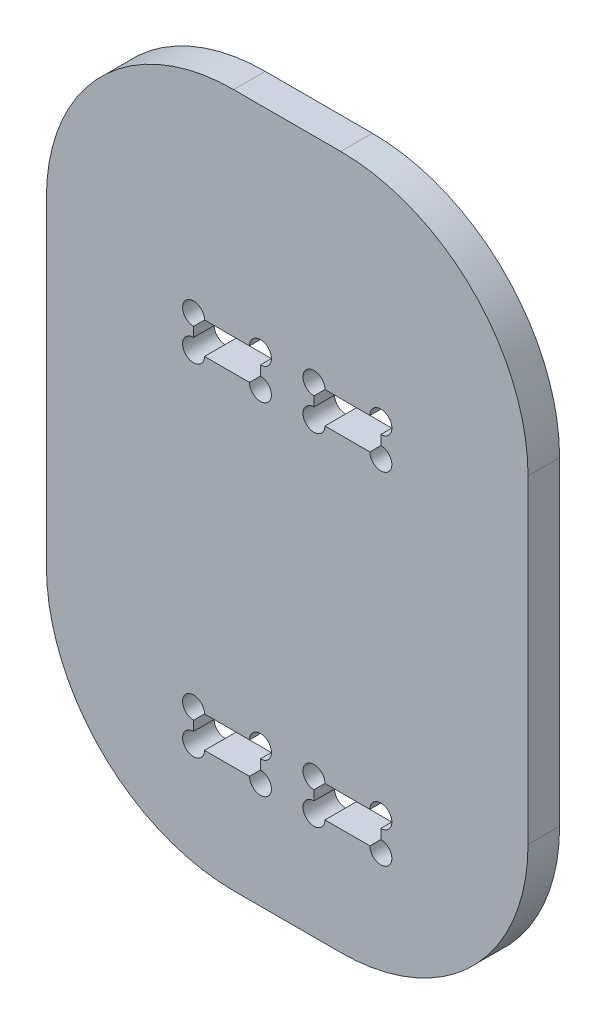
SolidWorks part; units mm, degrees
ref_plane "Front Plane" through (0, 0, 0) normal (0, 0, 1) x (1, 0, 0)
ref_plane "Top Plane" through (0, 0, 0) normal (0, 1, 0) x (1, 0, 0)
ref_plane "Right Plane" through (0, 0, 0) normal (1, 0, 0) x (0, 0, -1)
sketch "Sketch1" plane through (0, 0, 0) normal (0, 0, 1) x (1, 0, 0)
  line L0 (-17.5, 17.325) -> (17.5, 17.325) construction
  line L37 (-17.5, 17.325) -> (-17.5, -52.325) construction
  line L38 (-17.5, -52.325) -> (17.5, -52.325) construction
  line L39 (17.5, 17.325) -> (17.5, -52.325) construction
  line L40 (-17.5, 17.325) -> (17.5, -52.325) construction
  line L41 (-17.5, -52.325) -> (17.5, 17.325) construction
  line L42 (-17.5, 17.325) -> (-5, 17.325)
  line L43 (-17.5, 17.325) -> (-17.5, 11.425)
  line L44 (-17.5, 11.425) -> (-5, 11.425)
  line L45 (-5, 17.325) -> (-5, 11.425)
  line L46 (-17.5, 17.325) -> (-5, 11.425) construction
  line L47 (-17.5, 11.425) -> (-5, 17.325) construction
  line L48 (17.5, 17.325) -> (5, 17.325)
  line L49 (17.5, 17.325) -> (17.5, 11.425)
  line L50 (17.5, 11.425) -> (5, 11.425)
  line L51 (5, 17.325) -> (5, 11.425)
  line L52 (17.5, 17.325) -> (5, 11.425) construction
  line L53 (17.5, 11.425) -> (5, 17.325) construction
  line L54 (-45, -77.325) -> (45, -77.325)
  line L55 (17.5, -52.325) -> (5, -52.325)
  line L56 (17.5, -52.325) -> (17.5, -46.425)
  line L57 (17.5, -46.425) -> (5, -46.425)
  line L58 (5, -52.325) -> (5, -46.425)
  line L59 (17.5, -52.325) -> (5, -46.425) construction
  line L60 (17.5, -46.425) -> (5, -52.325) construction
  line L61 (-17.5, -52.325) -> (-5, -52.325)
  line L62 (-17.5, -52.325) -> (-17.5, -46.425)
  line L63 (-17.5, -46.425) -> (-5, -46.425)
  line L64 (-5, -52.325) -> (-5, -46.425)
  line L65 (-17.5, -52.325) -> (-5, -46.425) construction
  line L66 (-17.5, -46.425) -> (-5, -52.325) construction
  line L67 (-45, -77.325) -> (-45, 77.325)
  line L68 (-45, 77.325) -> (45, 77.325)
  line L69 (45, -77.325) -> (45, 77.325)
  line L70 (-45, -77.325) -> (45, 77.325) construction
  line L71 (-45, 77.325) -> (45, -77.325) construction
  point P30 (0, -17.5)
  point P32 (0, 0)
  point P35 (-11.25, 14.375)
  point P40 (11.25, 14.375)
  point P46 (11.25, -49.375)
  point P51 (-11.25, -49.375)
  dimension "D8" = 12.5
  dimension "D9" = 5.9
  dimension "D6" = 25
  dimension "D7" = 90
  dimension "D10" = 60
  dimension "D14" = 35
  dimension "D2" = 57.85
extrude "Boss-Extrude1" add sketch "Sketch1" along normal blind 5.9
fillet "Fillet2" radius 10 4 edges at (-45, -77.325, 2.95) (45, -77.325, 2.95) (45, 77.325, 2.95) (-45, 77.325, 2.95)
sketch "Sketch2" plane through (0, 0, 5.9) normal (0, 0, 1) x (1, 0, 0)
  line L0 (0, 0) -> (0, 77.325) construction
  line L1 (35, 77.325) -> (-35, 77.325) construction
  line L2 (-35, -77.325) -> (35, -77.325) construction
  line L3 (-10, -119.325) -> (10, -119.325) construction
  line L4 (-10, -119.325) -> (-10, -77.325) construction
  line L5 (-10, -77.325) -> (10, -77.325)
  line L6 (10, -119.325) -> (10, -77.325) construction
  line L7 (-10, -119.325) -> (10, -77.325) construction
  line L8 (-10, -77.325) -> (10, -119.325) construction
  line L17 (-48.9991, 110.2179) -> (-31.9041, 120.5986) construction
  line L18 (-48.9991, 110.2179) -> (-45.9144, 105.1379) construction
  line L19 (-31.9041, 120.5986) -> (-8.5475, 82.1347) construction
  line L23 (0, 77.325) -> (-13.9683, 77.325)
  line L25 (-45, 53.4823) -> (0, 77.325)
  line L26 (-45, 67.325) -> (-45, -67.325) construction
  line L33 (-38.5879, 93.0726) -> (-44.298, 113.0726)
  line L34 (-44.298, 113.0726) -> (-36.6052, 117.7439)
  line L35 (-36.6052, 117.7439) -> (-15.6534, 93.8367)
  line L36 (-15.6534, 93.8367) -> (-8.5475, 82.1347)
  line L38 (-10, -103.2393) -> (-4.5, -119.325)
  line L39 (-4.5, -119.325) -> (4.5, -119.325)
  line L40 (4.5, -119.325) -> (10, -103.2393)
  line L49 (-24.6, -77.325) -> (-10, -90.9393)
  line L50 (-10, -90.9393) -> (-10, -103.2393)
  line L51 (10, -103.2393) -> (10, -90.9393)
  line L52 (10, -90.9393) -> (24.6, -77.325)
  line L53 (-24.6, -77.325) -> (-10, -77.325)
  line L54 (10, -77.325) -> (24.6, -77.325)
  line L55 (-45, 53.4823) -> (-45, 67.325)
  line L57 (-38.5879, 93.0726) -> (-31.9704, 80.2418)
  line L58 (-35, 77.325) -> (-33.7479, 77.325)
  line L59 (45, 53.4823) -> (0, 77.325)
  line L60 (45, 53.4823) -> (45, 67.325)
  line L61 (35, 77.325) -> (33.7479, 77.325)
  line L62 (38.5879, 93.0726) -> (31.9704, 80.2418)
  line L63 (38.5879, 93.0726) -> (44.298, 113.0726)
  line L64 (44.298, 113.0726) -> (36.6052, 117.7439)
  line L65 (36.6052, 117.7439) -> (15.6534, 93.8367)
  line L66 (15.6534, 93.8367) -> (8.5475, 82.1347)
  arc A0 (-8.5475, 82.1347) -> (8.5475, 82.1347) centre (0, 87.325) ccw
  arc A4 (-35, 77.325) -> (-45, 67.325) centre (-35, 67.325) ccw construction
  arc A5 (-35, 77.325) -> (-45, 67.325) centre (-35, 67.325) ccw
  arc A6 (-31.9704, 80.2418) -> (-33.7479, 77.325) centre (-33.7479, 79.325) cw
  arc A7 (45, 67.325) -> (35, 77.325) centre (35, 67.325) ccw construction
  arc A8 (45, 67.325) -> (35, 77.325) centre (35, 67.325) ccw
  arc A9 (35, 77.325) -> (45, 67.325) centre (35, 67.325) cw
  arc A10 (31.9704, 80.2418) -> (33.7479, 77.325) centre (33.7479, 79.325) ccw
  point P5 (0, -98.325)
  point P13 (-40.4516, 115.4082)
  point P31 (0, -119.325)
  point P54 (-60, 0)
  dimension "D3" = 10
  dimension "D4" = 20
  dimension "D8" = 2
  dimension "D1" = 20
  dimension "D2" = 42
  dimension "D5" = 20
  dimension "D6" = 45
  dimension "D7" = 9
  dimension "D9" = 9
  dimension "D10" = 17
  dimension "D12" = 12.3
  dimension "D13" = 14.6
  dimension "D14" = 60
extrude "Boss-Extrude2" add sketch "Sketch2" against normal up to surface (5.9 mm away) up to face at (0, 0, 0)
sketch "Sketch4" plane through (0, 0, 5.9) normal (0, 0, 1) x (1, 0, 0)
  line L5 (0, 76.425) -> (0, 0) construction
sketch "Sketch5" plane through (0, 0, 5.9) normal (0, 0, 1) x (1, 0, 0)
  circle A0 centre (-17.5, 11.425) radius 2.05
  circle A1 centre (-5, 11.425) radius 2.05
  circle A2 centre (-5, 17.325) radius 2.05
  circle A3 centre (-17.5, 17.325) radius 2.05
  circle A4 centre (17.5, 11.425) radius 2.05
  circle A5 centre (17.5, 17.325) radius 2.05
  circle A6 centre (5, 17.325) radius 2.05
  circle A7 centre (5, 11.425) radius 2.05
  circle A8 centre (5, -52.325) radius 2.05
  circle A9 centre (17.5, -52.325) radius 2.05
  circle A10 centre (17.5, -46.425) radius 2.05
  circle A11 centre (5, -46.425) radius 2.05
  circle A12 centre (-5, -46.425) radius 2.05
  circle A13 centre (-5, -52.325) radius 2.05
  circle A14 centre (-17.5, -52.325) radius 2.05
  circle A15 centre (-17.5, -46.425) radius 2.05
  dimension "D1" = 4.1
extrude "Cut-Extrude1" cut sketch "Sketch5" against normal up to next
sketch "Sketch7" plane through (0, 0, 5.9) normal (0, 0, 1) x (1, 0, 0)
  line L0 (-45, 67.325) -> (-45, -67.325) construction
  line L1 (-45, -72.325) -> (45, -72.325)
  line L2 (-45, -72.325) -> (-45, 57.325)
  line L3 (-45, 57.325) -> (45, 57.325)
  line L4 (45, -72.325) -> (45, 57.325)
  line L5 (-45, -72.325) -> (45, 57.325) construction
  line L6 (-45, 57.325) -> (45, -72.325) construction
  line L7 (45, -67.325) -> (45, 67.325) construction
  line L8 (24.6, -77.325) -> (35, -77.325) construction
  line L9 (-33.7479, 77.325) -> (-35, 77.325) construction
  line L33 (-45, 67.325) -> (-45, -67.325)
  line L34 (-35, -77.325) -> (-24.6, -77.325)
  line L35 (-24.6, -77.325) -> (-10, -90.9393)
  line L36 (-10, -90.9393) -> (-10, -103.2393)
  line L37 (-10, -103.2393) -> (-4.5, -119.325)
  line L38 (-4.5, -119.325) -> (4.5, -119.325)
  line L39 (4.5, -119.325) -> (10, -103.2393)
  line L40 (10, -103.2393) -> (10, -90.9393)
  line L41 (10, -90.9393) -> (24.6, -77.325)
  line L42 (24.6, -77.325) -> (35, -77.325)
  line L43 (45, -67.325) -> (45, 67.325)
  line L44 (35, 77.325) -> (33.7479, 77.325)
  line L45 (31.9704, 80.2418) -> (38.5879, 93.0726)
  line L46 (38.5879, 93.0726) -> (44.298, 113.0726)
  line L47 (44.298, 113.0726) -> (36.6052, 117.7439)
  line L48 (36.6052, 117.7439) -> (15.6534, 93.8367)
  line L49 (15.6534, 93.8367) -> (8.5475, 82.1347)
  line L50 (-8.5475, 82.1347) -> (-15.6534, 93.8367)
  line L51 (-15.6534, 93.8367) -> (-36.6052, 117.7439)
  line L52 (-36.6052, 117.7439) -> (-44.298, 113.0726)
  line L53 (-44.298, 113.0726) -> (-38.5879, 93.0726)
  line L54 (-38.5879, 93.0726) -> (-31.9704, 80.2418)
  line L55 (-33.7479, 77.325) -> (-35, 77.325)
  line L56 (-45, 67.325) -> (-45, -67.325)
  line L57 (-35, -77.325) -> (-24.6, -77.325)
  line L58 (-24.6, -77.325) -> (-10, -90.9393)
  line L59 (-10, -90.9393) -> (-10, -103.2393)
  line L60 (-10, -103.2393) -> (-4.5, -119.325)
  line L61 (-4.5, -119.325) -> (4.5, -119.325)
  line L62 (4.5, -119.325) -> (10, -103.2393)
  line L63 (10, -103.2393) -> (10, -90.9393)
  line L64 (10, -90.9393) -> (24.6, -77.325)
  line L65 (24.6, -77.325) -> (35, -77.325)
  line L66 (45, -67.325) -> (45, 67.325)
  line L67 (35, 77.325) -> (33.7479, 77.325)
  line L68 (31.9704, 80.2418) -> (38.5879, 93.0726)
  line L69 (38.5879, 93.0726) -> (44.298, 113.0726)
  line L70 (44.298, 113.0726) -> (36.6052, 117.7439)
  line L71 (36.6052, 117.7439) -> (15.6534, 93.8367)
  line L72 (15.6534, 93.8367) -> (8.5475, 82.1347)
  line L73 (-8.5475, 82.1347) -> (-15.6534, 93.8367)
  line L74 (-15.6534, 93.8367) -> (-36.6052, 117.7439)
  line L75 (-36.6052, 117.7439) -> (-44.298, 113.0726)
  line L76 (-44.298, 113.0726) -> (-38.5879, 93.0726)
  line L77 (-38.5879, 93.0726) -> (-31.9704, 80.2418)
  line L78 (-33.7479, 77.325) -> (-35, 77.325)
  arc A7 (-45, -67.325) -> (-35, -77.325) centre (-35, -67.325) ccw
  arc A8 (35, -77.325) -> (45, -67.325) centre (35, -67.325) ccw
  arc A9 (45, 67.325) -> (35, 77.325) centre (35, 67.325) ccw
  arc A10 (31.9704, 80.2418) -> (33.7479, 77.325) centre (33.7479, 79.325) ccw
  arc A11 (-8.5475, 82.1347) -> (8.5475, 82.1347) centre (0, 87.325) ccw
  arc A12 (-33.7479, 77.325) -> (-31.9704, 80.2418) centre (-33.7479, 79.325) ccw
  arc A13 (-35, 77.325) -> (-45, 67.325) centre (-35, 67.325) ccw
  arc A14 (-45, -67.325) -> (-35, -77.325) centre (-35, -67.325) ccw
  arc A15 (35, -77.325) -> (45, -67.325) centre (35, -67.325) ccw
  arc A16 (45, 67.325) -> (35, 77.325) centre (35, 67.325) ccw
  arc A17 (31.9704, 80.2418) -> (33.7479, 77.325) centre (33.7479, 79.325) ccw
  arc A18 (-8.5475, 82.1347) -> (8.5475, 82.1347) centre (0, 87.325) ccw
  arc A19 (-33.7479, 77.325) -> (-31.9704, 80.2418) centre (-33.7479, 79.325) ccw
  arc A20 (-35, 77.325) -> (-45, 67.325) centre (-35, 67.325) ccw
  point P4 (0, -7.5)
  dimension "D1" = 5
  dimension "D2" = 20
  dimension "D3" = 0
extrude "Cut-Extrude4" cut sketch "Sketch7" against normal up to next contours L78 A20 L56 L3 L66 A16 L67 A17 L68 L69 L70 L71 L72 A18 L73 L74 L75 L76 L77 A19 | L65 A15 L1 A14 L57 L58 L59 L60 L61 L62 L63 L64
fillet "Fillet3" radius 35 4 edges at (43.6603, -72.325, 2.95) (-43.6603, -72.325, 2.95) (45, 57.325, 2.95) (-45, 57.325, 2.95)
equation "\"e\" = 5.9"
equation "\"D1@Boss-Extrude1\"= \"e\""
equation "\"D9@Sketch1\"= \"e\""
